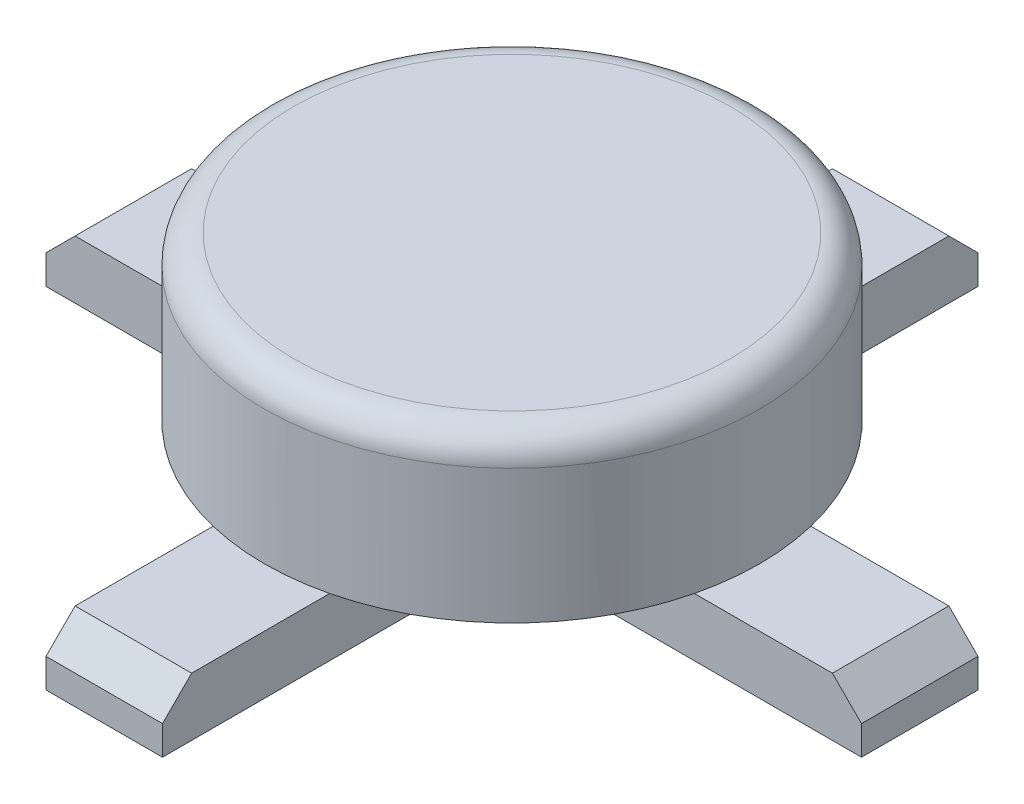
SolidWorks part; units mm, degrees
ref_plane "前视基准面" through (0, 0, 0) normal (0, 0, 1) x (1, 0, 0)
ref_plane "上视基准面" through (0, 0, 0) normal (0, 1, 0) x (1, 0, 0)
ref_plane "右视基准面" through (0, 0, 0) normal (1, 0, 0) x (0, 0, -1)
sketch "草图1" plane through (0, 0, 0) normal (0, 1, 0) x (1, 0, 0)
  circle A0 centre (0, 0) radius 4.25
  dimension "D1" = 8.5
extrude "凸台-拉伸1" add sketch "草图1" along normal blind 2.8
fillet "圆角1" radius 0.5 1 edges at (0, 2.8, 4.25)
sketch "草图2" plane through (0, 0, 0) normal (0, -1, 0) x (1, 0, 0)
  line L1 (-7, 1) -> (7, 1)
  line L2 (-7, 1) -> (-7, -1)
  line L3 (-7, -1) -> (7, -1)
  line L4 (7, 1) -> (7, -1)
  line L5 (-7, 1) -> (7, -1) construction
  line L6 (-7, -1) -> (7, 1) construction
  circle A0 centre (0, 0) radius 4.25 construction
  point P6 (0, 0)
  dimension "D1" = 2
  dimension "D2" = 14
extrude "凸台-拉伸2" add sketch "草图2" along normal blind 1
sketch "草图3" plane through (0, 0, 0) normal (0, -1, 0) x (1, 0, 0)
  line L1 (-1, 7) -> (1, 7)
  line L2 (-1, 7) -> (-1, -7)
  line L3 (-1, -7) -> (1, -7)
  line L4 (1, 7) -> (1, -7)
  line L5 (-1, 7) -> (1, -7) construction
  line L6 (-1, -7) -> (1, 7) construction
  arc A0 (4.1307, 1) -> (-4.1307, 1) centre (0, 0) ccw construction
  point P7 (0, 0)
  dimension "D1" = 14
  dimension "D2" = 2
extrude "凸台-拉伸3" add sketch "草图3" along normal blind 1
chamfer "倒角1" distance 0.5 angle 45 1 edges at (0, 0, 7)
chamfer "倒角2" distance 0.5 angle 45 1 edges at (7, 0, 0)
chamfer "倒角3" distance 0.5 angle 45 2 edges at (-7, 0, 0) (0, 0, -7)
